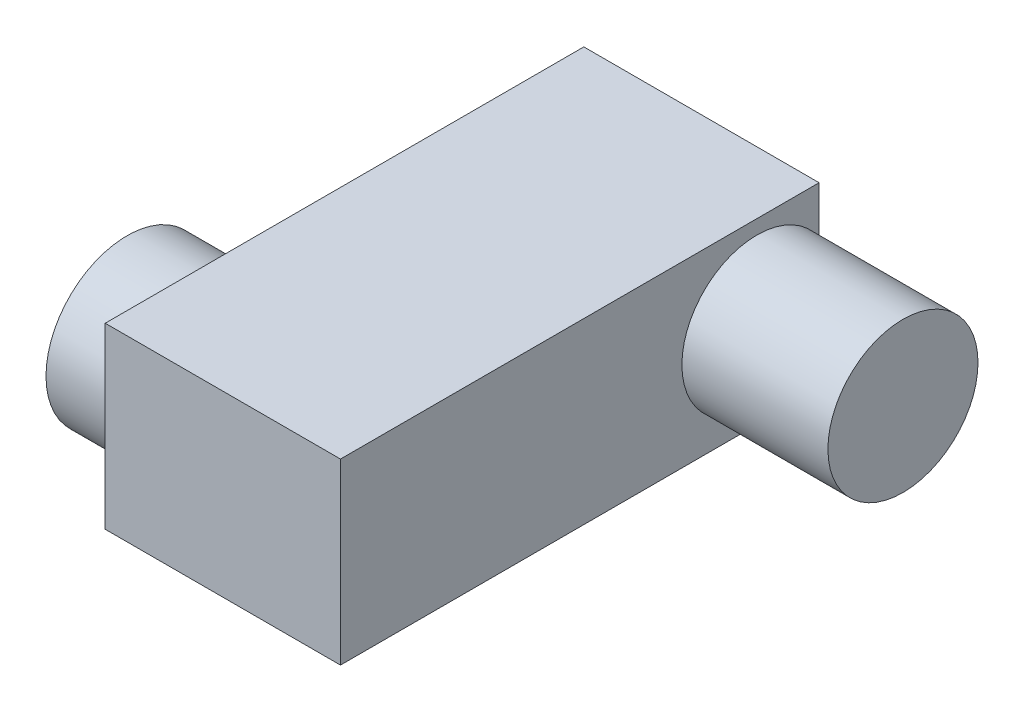
SolidWorks part; units mm, degrees
ref_plane "Front Plane" through (0, 0, 0) normal (0, 0, 1) x (1, 0, 0)
ref_plane "Top Plane" through (0, 0, 0) normal (0, 1, 0) x (1, 0, 0)
ref_plane "Right Plane" through (0, 0, 0) normal (1, 0, 0) x (0, 0, -1)
sketch "Sketch1" plane through (0, 0, 0) normal (0, 1, 0) x (1, 0, 0)
  line L22 (0, 0) -> (-29, 0)
  line L23 (0, 0) -> (0, 59)
  line L24 (0, 59) -> (-29, 59)
  line L39 (-29, 0) -> (-29, 59)
  point P0 (0, 0)
  dimension "D3" = 29
  dimension "D4" = 59
extrude "Boss-Extrude1" add sketch "Sketch1" along normal blind 22
sketch "Sketch4" plane through (0, 0, 0) normal (1, 0, 0) x (0, 0, -1)
  line L1 (59, 22) -> (59, 0) construction
  circle A0 centre (51.3375, 11) radius 9.25
  point P7 (59, 11)
  dimension "D1" = 18.5
  dimension "D3" = 1.5875
extrude "Boss-Extrude4" add sketch "Sketch4" along normal blind 18
sketch "Sketch5" plane through (-29, 0, 0) normal (-1, 0, 0) x (0, 0, 1)
  line L0 (0, 22) -> (0, 0) construction
  circle A0 centre (-11.7, 11) radius 10
  point P5 (0, 11)
  dimension "D1" = 20
  dimension "D2" = 1.7
extrude "Boss-Extrude5" add sketch "Sketch5" along normal blind 9
